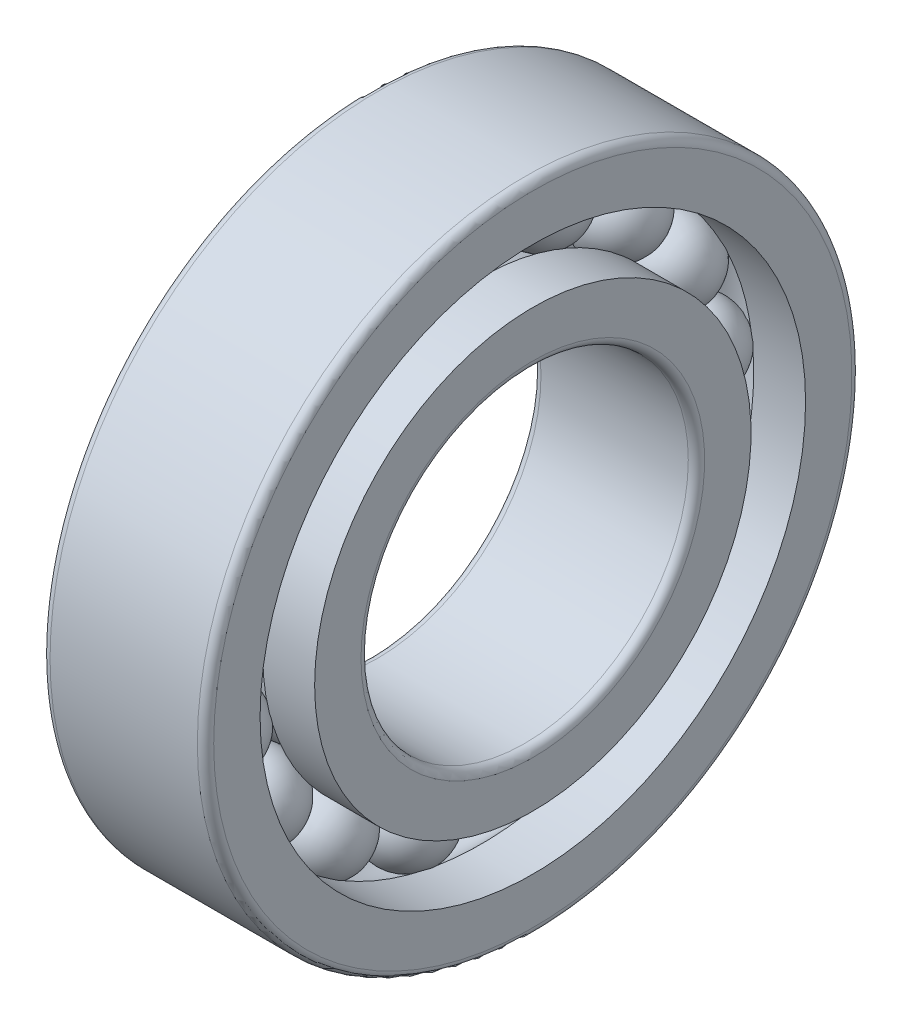
SolidWorks part; units mm, degrees
ref_plane "Front" through (0, 0, 0) normal (0, 0, 1) x (1, 0, 0)
ref_plane "Top" through (0, 0, 0) normal (0, 1, 0) x (1, 0, 0)
ref_plane "Right" through (0, 0, 0) normal (1, 0, 0) x (0, 0, -1)
sketch "Sketch1" plane through (0, 0, 0) normal (0, 0, 1) x (1, 0, 0)
  line L0 (-9.6833, 0) -> (9.8371, 0) construction
  line L1 (-1, 6) -> (1, 6)
  line L2 (-4.5966, 6) -> (4.6657, 6) construction
  arc A0 (1, 6) -> (-1, 6) centre (0, 6) ccw
  dimension "dia" = 2
  dimension "d0" = 12
revolve "Revolve1" add sketch "Sketch1" angle 360 about L2
sketch "Sketch2" plane through (0, 0, 0) normal (0, 0, 1) x (1, 0, 0)
  line L0 (-2, 5.3333) -> (-2, 4)
  line L1 (-2, 4) -> (2, 4)
  line L2 (2, 4) -> (2, 5.3333)
  line L3 (2, 5.3333) -> (0.7319, 5.3333)
  line L4 (-6.9714, 0) -> (8.1665, 0) construction
  line L5 (-6.7058, 6) -> (6.7058, 6) construction
  line L6 (-0.7319, 5.3333) -> (-2, 5.3333)
  arc A0 (-0.7319, 5.3333) -> (0.7319, 5.3333) centre (0, 6) ccw
  dimension "B" = 4
  dimension "B/2" = 2
  dimension "D5" = 1.98
  dimension "d" = 8
  dimension "D3" = 6
  dimension "D4" = 1.3333
revolve "Revolve2" add sketch "Sketch2" angle 360 about L4
sketch "Sketch3" plane through (0, 0, 0) normal (0, 0, 1) x (1, 0, 0)
  line L0 (-8.7107, 0) -> (9.1288, 0) construction
  line L1 (-2, 8) -> (2, 8)
  line L2 (-2, 8) -> (-2, 6.6667)
  line L3 (-2, 6.6667) -> (-0.7319, 6.6667)
  line L4 (2, 8) -> (2, 6.6667)
  line L5 (-7.2948, 6) -> (7.2948, 6) construction
  line L6 (0.7319, 6.6667) -> (2, 6.6667)
  arc A0 (0.7319, 6.6667) -> (-0.7319, 6.6667) centre (0, 6) ccw
  dimension "D1" = 1.98
  dimension "DD" = 16
  dimension "B" = 4
  dimension "D4" = 6
  dimension "D5" = 1.3333
  dimension "B/2" = 2
revolve "Revolve3" add sketch "Sketch3" angle 360 about L0
pattern_circular "Circular-Pattern1" count 17 over 360 about axis through (0, 0, 0) along (1, 0, 0) of "Revolve1"
fillet "Fillet1" radius 0.2 4 edges at (-2, 0, 4) (-2, 0, 8) (2, 0, 8) (2, 0, 4)
equation "\"d0@Sketch1\" = ( \"DD@Sketch3\" + \"d@Sketch2\" )  / 2"
equation "\"dia@Sketch1\" =  ( \"DD@Sketch3\" - \"d@Sketch2\" )  / 4"
equation "\"D3@Sketch2\" = ( \"DD@Sketch3\" + \"d@Sketch2\" )  / 2 / 2"
equation "\"D4@Sketch2\" = ( \"DD@Sketch3\" - \"d@Sketch2\" )  / 6"
equation "\"D5@Sketch2\" = \"dia@Sketch1\" - 0.02"
equation "\"B/2@Sketch2\" = \"B@Sketch2\" / 2"
equation "\"D4@Sketch3\" = ( \"DD@Sketch3\" + \"d@Sketch2\" )  / 2 / 2"
equation "\"D5@Sketch3\" = ( \"DD@Sketch3\" - \"d@Sketch2\" )  / 6"
equation "\"B@Sketch3\" = \"B@Sketch2\""
equation "\"B/2@Sketch3\" = \"B@Sketch3\" / 2"
equation "\"D1@Sketch3\" = \"dia@Sketch1\" - 0.02"
equation "\"m@Circular-Pattern1\" = int( 3.14159265 / atn(( \"dia@Sketch1\" / 2) / sqr(( \"DD@Sketch3\" + \"d@Sketch2\" )  / 2 * ( \"DD@Sketch3\" + \"d@Sketch2\" )  / 2/4 - ( \"dia@Sketch1\" / 2) *  ( \"dia@Sketch1\" / 2))))-1"
